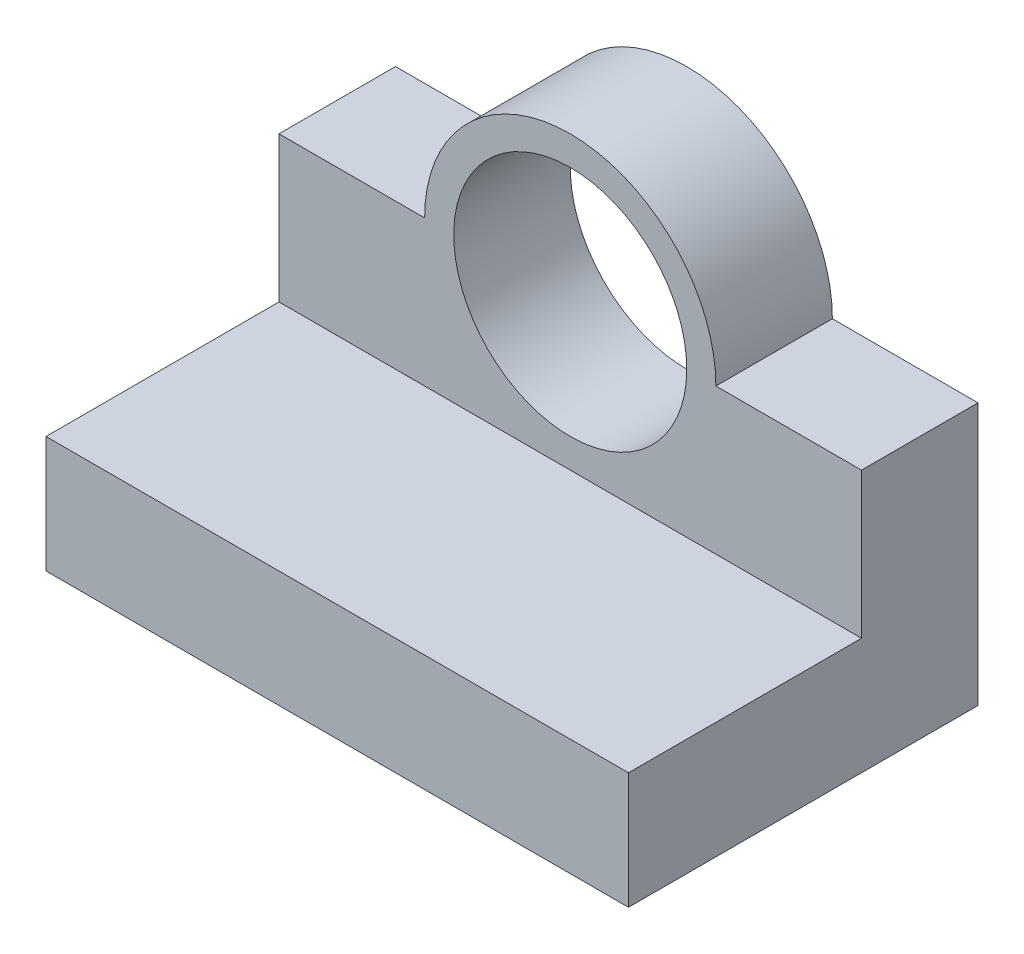
SolidWorks part; units mm, degrees
ref_plane "Front Plane" through (0, 0, 0) normal (0, 0, 1) x (1, 0, 0)
ref_plane "Top Plane" through (0, 0, 0) normal (0, 1, 0) x (1, 0, 0)
ref_plane "Right Plane" through (0, 0, 0) normal (1, 0, 0) x (0, 0, -1)
sketch "Sketch1" plane through (0, 0, 0) normal (1, 0, 0) x (0, 0, -1)
  line L0 (10, 35) -> (10, -15)
  line L1 (-30, -35) -> (30, -35)
  line L2 (-30, -35) -> (-30, -15)
  line L3 (10, 35) -> (30, 35)
  line L4 (30, -35) -> (30, 35)
  line L5 (-30, -35) -> (0, 0) construction
  line L6 (0, 0) -> (10, -11.6667) construction
  line L7 (-30, -15) -> (10, -15)
  point P0 (0, 0)
  dimension "D1" = 60
  dimension "D2" = 70
  dimension "D3" = 20
  dimension "D4" = 20
extrude "Boss-Extrude1" add sketch "Sketch1" along normal blind 100
sketch "Sketch2" plane through (0, 0, -10) normal (0, 0, 1) x (1, 0, 0)
  line L0 (50, 38.7566) -> (50, -12.7642) construction
  line L1 (0, 35) -> (0, -15) construction
  line L2 (-1.5805, 10) -> (4.5982, 10) construction
  line L3 (0, 10) -> (25, 10)
  line L4 (75, 10) -> (100, 10)
  line L6 (0, 10) -> (0, 35)
  line L7 (100, 35) -> (0, 35)
  line L8 (100, 35) -> (100, 10)
  line L9 (100, 35) -> (100, -15) construction
  arc A1 (75, 10) -> (25, 10) centre (50, 10) ccw
  line M3 (0, 35) -> (0, -15)
  line M5 (100, -15) -> (100, 35)
  line M6 (100, 35) -> (0, 35)
  dimension "D3" = 50
  dimension "D1" = 50
  dimension "D2" = 45
extrude "Cut-Extrude1" cut sketch "Sketch2" against normal through all contours A1 L7 L3 M3 | A1 L4 M5 M6
sketch "Sketch3" plane through (0, 0, -10) normal (0, 0, 1) x (1, 0, 0)
  line L0 (25, 10) -> (3.8346, 10)
  line L1 (0, 10) -> (25, 10) construction
  line L2 (3.8346, 10) -> (25, 10)
  line L4 (50, 26.2245) -> (50, 10)
  circle A0 centre (50, 10) radius 20
  dimension "D2" = 40
  dimension "D1" = 50
extrude "Cut-Extrude3" cut sketch "Sketch3" against normal through all and the other way through all
